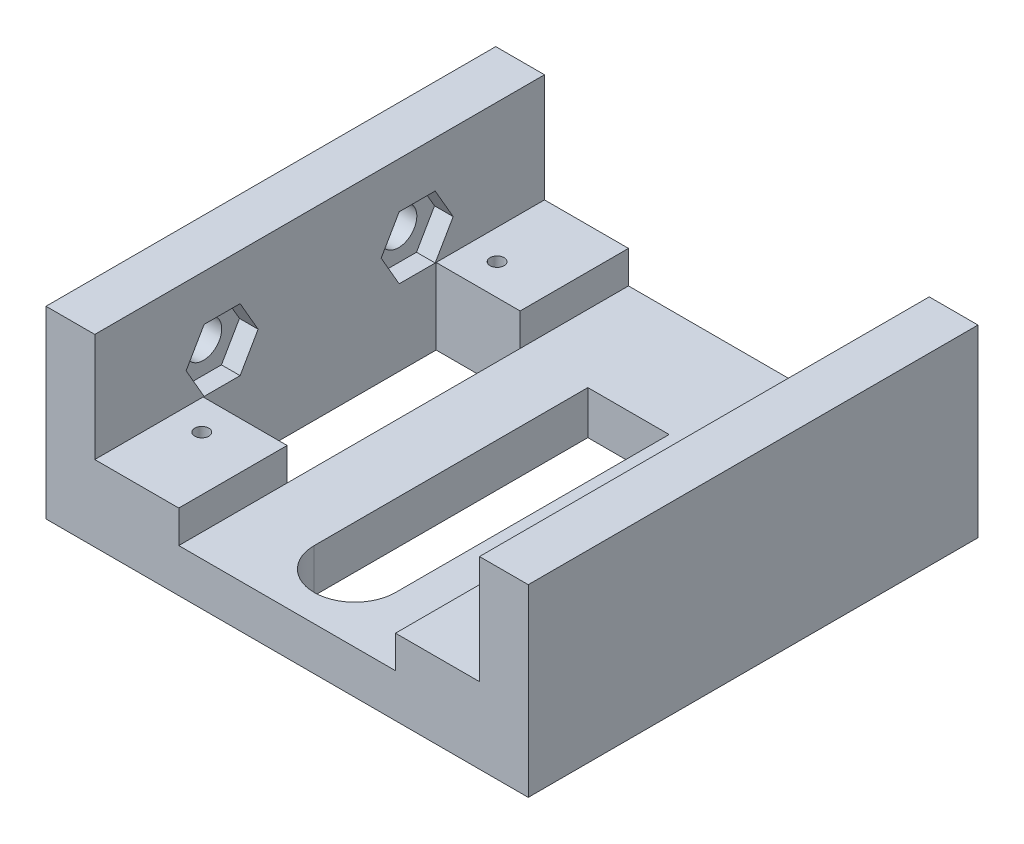
SolidWorks part; units mm, degrees
ref_plane "Front Plane" through (0, 0, 0) normal (0, 0, 1) x (1, 0, 0)
ref_plane "Top Plane" through (0, 0, 0) normal (0, 1, 0) x (1, 0, 0)
ref_plane "Right Plane" through (0, 0, 0) normal (1, 0, 0) x (0, 0, -1)
sketch "Sketch1" plane through (0, 0, 0) normal (0, 1, 0) x (1, 0, 0)
  line L0 (-7.5, 12.5) -> (-7.5, 63)
  line L9 (-44.5, 0) -> (44.5, 0)
  line L10 (-44.5, 0) -> (-44.5, 83)
  line L11 (-44.5, 83) -> (44.5, 83)
  line L12 (44.5, 0) -> (44.5, 83)
  line L13 (34.5, 0) -> (-34.5, 0) construction
  line L14 (34.5, 0) -> (34.5, 83) construction
  line L15 (34.5, 83) -> (-34.5, 83) construction
  line L16 (-34.5, 0) -> (-34.5, 83) construction
  line L17 (-7.5, 5) -> (0, 5) construction
  line L18 (-7.5, 5) -> (-7.5, 12.5) construction
  line L19 (-7.5, 63) -> (7.5, 63)
  line L20 (7.5, 5) -> (7.5, 12.5) construction
  line L21 (-30, 14.25) -> (30, 14.25) construction
  line L22 (-30, 14.25) -> (-30, 68.75) construction
  line L23 (-30, 68.75) -> (30, 68.75) construction
  line L24 (30, 14.25) -> (30, 68.75) construction
  line L25 (7.5, 12.5) -> (7.5, 63)
  line L26 (0, 5) -> (7.5, 5)
  circle A0 centre (30, 14.25) radius 1.3
  circle A1 centre (-30, 14.25) radius 1.3
  circle A2 centre (-30, 68.75) radius 1.3
  circle A3 centre (30, 68.75) radius 1.3
  circle A4 centre (-30, 68.75) radius 1.75 construction
  circle A5 centre (0, 12.5) radius 7.5
  point P9 (0, 0)
  point P10 (0, 0)
  point P25 (0, 14.25)
  point P27 (44.5, 41.5)
  point P28 (30, 41.5)
  point P30 (-3.3924, 8.0955)
  point P33 (0, 0)
  point P34 (7.5, 17.5594)
  point P35 (7.5, 12.5)
  point P36 (-7.5, 12.5)
  dimension "D7" = 2.6
  dimension "D8" = 3.5
  dimension "D1" = 83
  dimension "D2" = 69
  dimension "D3" = 10
  dimension "D4" = 15
  dimension "D5" = 20
  dimension "D6" = 5
  dimension "D9" = 60
  dimension "D10" = 54.5
extrude "Main Body" add sketch "Sketch1" along normal blind 14 contours L9 L12 L11 L10 A3 A2 A1 A0 L20 L17 L18 L19
sketch "Sketch2" plane through (0, 14, 0) normal (0, 1, 0) x (1, 0, 0)
  line L1 (-20, 0) -> (20, 0)
  line L2 (-20, 0) -> (-20, 83)
  line L3 (-20, 83) -> (20, 83)
  line L4 (20, 0) -> (20, 83)
  line L7 (-44.5, 83) -> (44.5, 83) construction
  point P8 (0, 0)
  dimension "D1" = 40
extrude "Screw Groove" cut sketch "Sketch2" against normal blind 6
sketch "Sketch4" plane through (0, 14, 0) normal (0, 1, 0) x (1, 0, 0)
  line L0 (-44.5, 0) -> (-20, 0) construction
  line L1 (-44.5, 83) -> (-35.5, 83)
  line L2 (-44.5, 83) -> (-44.5, 0)
  line L3 (-44.5, 0) -> (-35.5, 0)
  line L4 (-35.5, 83) -> (-35.5, 0)
  line L5 (20, 83) -> (44.5, 83) construction
  line L6 (44.5, 0) -> (35.5, 0)
  line L7 (44.5, 0) -> (44.5, 83)
  line L8 (44.5, 83) -> (35.5, 83)
  line L9 (35.5, 0) -> (35.5, 83)
  dimension "D1" = 71
extrude "Mount Lift" add sketch "Sketch4" along normal offset from surface (20 mm away) 34 up to face at (0, 0, -35.875)
ref_plane "Plane1" through (-38.9438, 0, 0) normal (-1, 0, 0) x (0, 0, 1)
sketch "Sketch6" plane through (-44.5, 0, 0) normal (-1, 0, 0) x (0, 0, 1)
  line L0 (-52.8551, 19.7547) -> (-56.1775, 25.5094)
  line L1 (-53.0842, 19.7547) -> (-56.2921, 25.3109) construction
  line L2 (-56.2921, 25.3109) -> (-62.7079, 25.3109) construction
  line L3 (-62.7079, 25.3109) -> (-65.9158, 19.7547) construction
  line L4 (-65.9158, 19.7547) -> (-62.7079, 14.1984) construction
  line L5 (-62.7079, 14.1984) -> (-56.2921, 14.1984) construction
  line L6 (-56.2921, 14.1984) -> (-53.0842, 19.7547) construction
  line L7 (-56.1775, 25.5094) -> (-62.8225, 25.5094)
  line L8 (-62.8225, 25.5094) -> (-66.1449, 19.7547)
  line L9 (-66.1449, 19.7547) -> (-62.8225, 14)
  line L10 (-62.8225, 14) -> (-56.1775, 14)
  line L11 (-56.1775, 14) -> (-52.8551, 19.7547)
  line L12 (-23.5, 19.7547) -> (-59.5, 19.7547) construction
  line L13 (-16.8551, 19.7547) -> (-20.1775, 25.5094)
  line L14 (-20.1775, 25.5094) -> (-26.8225, 25.5094)
  line L15 (-26.8225, 25.5094) -> (-30.1449, 19.7547)
  line L16 (-30.1449, 19.7547) -> (-26.8225, 14)
  line L17 (-26.8225, 14) -> (-20.1775, 14)
  line L18 (-20.1775, 14) -> (-16.8551, 19.7547)
  line L19 (0, 0) -> (-83, 0) construction
  line L23 (-12.95, 14) -> (-15.55, 14) construction
  circle A0 centre (-59.5, 19.7547) radius 5.5563 construction
  circle A1 centre (-23.5, 19.7547) radius 5.7547 construction
  point P26 (-41.5, 0)
  point P27 (-41.5, 19.7547)
  dimension "D1" = 11.1125
  dimension "D3" = 36
  dimension "D2" = 0.1984
extrude "Mount Nuts" cut sketch "Sketch6" against normal up to surface (18.9438 mm away) from surface at -5.5563 up to face at (-20, 11, -41.5) starting at plane "Plane1"
sketch "Sketch5" plane through (-38.9438, 0, 0) normal (-1, 0, 0) x (0, 0, 1)
  line L0 (0, 0) -> (-83, 0) construction
  line L1 (-20.1775, 14) -> (-26.8225, 25.5094) construction
  line L4 (-59.5, 19.7547) -> (-23.5, 19.7547) construction
  circle A0 centre (-59.5, 19.7547) radius 3.175 construction
  circle A1 centre (-23.5, 19.7547) radius 3.175 construction
  circle A2 centre (-59.5, 19.7547) radius 3.3734
  circle A3 centre (-23.5, 19.7547) radius 3.3734
  circle A4 centre (-23.5, 19.7547) radius 7.9375 construction
  circle A5 centre (-59.5, 19.7547) radius 7.9375 construction
  point P2 (-23.5, 19.7547)
  point P3 (-41.5, 0)
  point P4 (-41.5, 19.7547)
  dimension "D2" = 6.35
  dimension "D5" = 15.875
  dimension "D3" = 0.1984
extrude "9/32 Mount Holes" cut sketch "Sketch5" along normal up to next
sketch "Sketch8" plane through (0, 14, 0) normal (0, 1, 0) x (1, 0, 0)
  line L33 (-20, 0) -> (20, 0) construction
  line L34 (-35.5, 20) -> (35.5, 20) construction
  line L35 (-35.5, 20) -> (-35.5, 63) construction
  line L36 (-35.5, 63) -> (35.5, 63) construction
  line L37 (35.5, 20) -> (35.5, 63) construction
  line L38 (20, 83) -> (-20, 83) construction
  line L39 (35.5, 83) -> (35.5, 0) construction
  line L40 (-35.5, 0) -> (-35.5, 83) construction
  line L41 (-20, 83) -> (-20, 0) construction
  line L42 (-35.5, 63) -> (-20, 63)
  line L43 (-35.5, 63) -> (-35.5, 20)
  line L44 (-35.5, 20) -> (-20, 20)
  line L45 (-20, 63) -> (-20, 20)
  line L46 (20, 0) -> (20, 83) construction
  line L47 (35.5, 63) -> (20, 63)
  line L48 (35.5, 63) -> (35.5, 20)
  line L49 (35.5, 20) -> (20, 20)
  line L50 (20, 63) -> (20, 20)
  dimension "D1" = 20
  dimension "D2" = 20
extrude "Middle Cut" cut sketch "Sketch8" against normal up to surface (14 mm away) up to face at (0, 0, -35.875)
